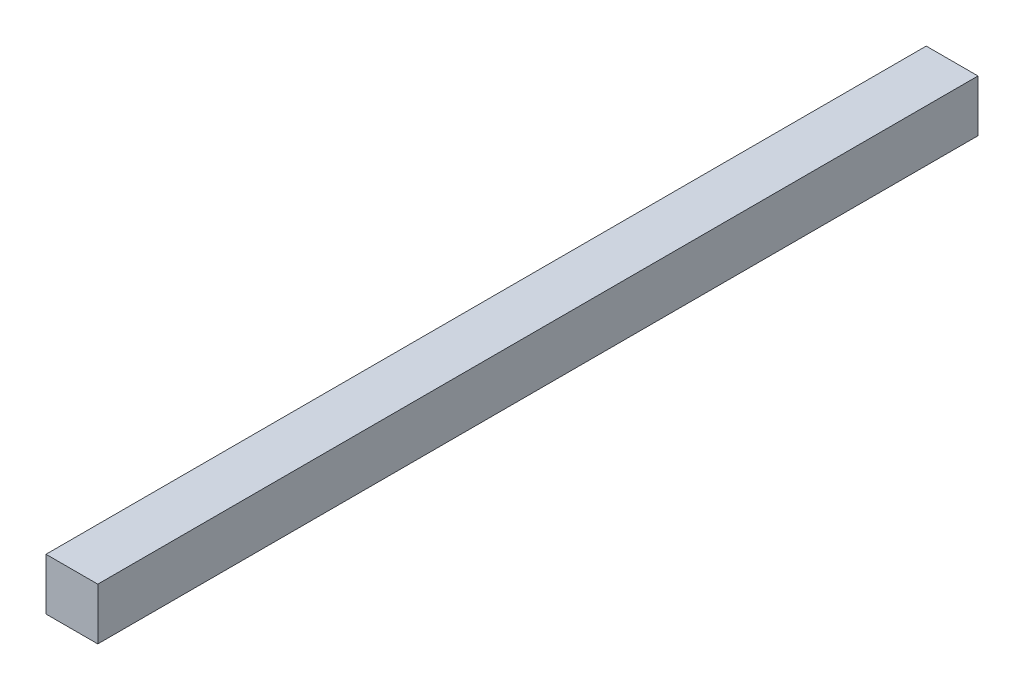
SolidWorks part; units mm, degrees
ref_plane "Front Plane" through (0, 0, 0) normal (0, 0, 1) x (1, 0, 0)
ref_plane "Top Plane" through (0, 0, 0) normal (0, 1, 0) x (1, 0, 0)
ref_plane "Right Plane" through (0, 0, 0) normal (1, 0, 0) x (0, 0, -1)
sketch "Sketch1" plane through (0, 0, 0) normal (0, 0, 1) x (1, 0, 0)
  line L1 (0, 0) -> (25.4, 0)
  line L2 (0, 0) -> (0, 25.4)
  line L3 (0, 25.4) -> (25.4, 25.4)
  line L4 (25.4, 0) -> (25.4, 25.4)
  dimension "D1" = 25.4
  dimension "D2" = 25.4
extrude "Boss-Extrude1" add sketch "Sketch1" along normal blind 431.8
